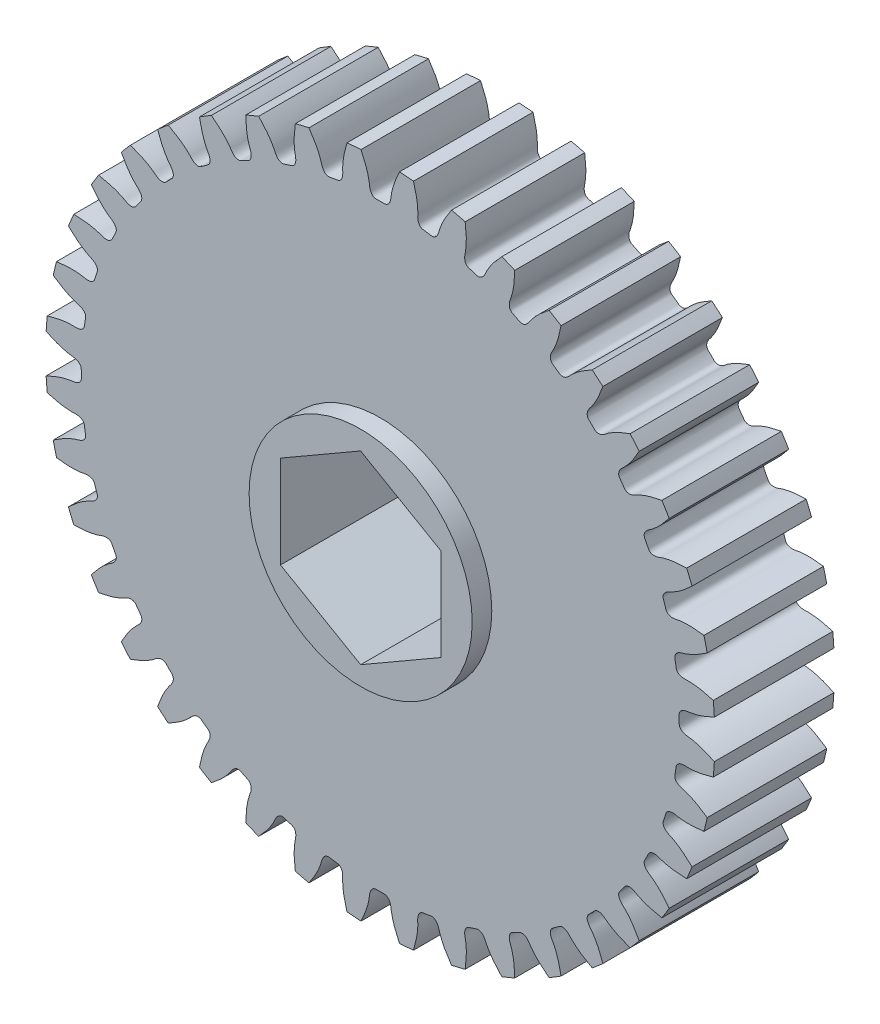
SolidWorks part; units mm, degrees
material "7075-T6 (SN)"
ref_plane "Front Plane" through (0, 0, 0) normal (0, 0, 1) x (1, 0, 0)
ref_plane "Top Plane" through (0, 0, 0) normal (0, 1, 0) x (1, 0, 0)
ref_plane "Right Plane" through (0, 0, 0) normal (1, 0, 0) x (0, 0, -1)
ref_plane "Plane1" through (0, 0, -4.7625) normal (0, 0, -1) x (-1, 0, 0)
sketch "Sketch1" plane through (0, 0, -4.7625) normal (0, 0, -1) x (-1, 0, 0)
  arc A0 (-25.7968, 6.7684) -> (-26.058, 5.6808) centre (0, 0) ccw
  arc A1 (-26.5381, 2.6496) -> (-26.6258, 1.5345) centre (0, 0) ccw
  arc A2 (-26.6258, -1.5345) -> (-26.5381, -2.6496) centre (0, 0) ccw
  arc A3 (-26.058, -5.6808) -> (-25.7968, -6.7684) centre (0, 0) ccw
  arc A4 (-24.8485, -9.6872) -> (-24.4204, -10.7206) centre (0, 0) ccw
  arc A5 (-23.0271, -13.4551) -> (-22.4427, -14.4088) centre (0, 0) ccw
  arc A6 (-20.6388, -16.8917) -> (-19.9124, -17.7422) centre (0, 0) ccw
  arc A7 (-17.7422, -19.9124) -> (-16.8917, -20.6388) centre (0, 0) ccw
  arc A8 (-14.4088, -22.4427) -> (-13.4551, -23.0271) centre (0, 0) ccw
  arc A9 (-10.7206, -24.4204) -> (-9.6872, -24.8485) centre (0, 0) ccw
  arc A10 (-6.7684, -25.7968) -> (-5.6808, -26.058) centre (0, 0) ccw
  arc A11 (-2.6496, -26.5381) -> (-1.5345, -26.6258) centre (0, 0) ccw
  arc A12 (1.5345, -26.6258) -> (2.6496, -26.5381) centre (0, 0) ccw
  arc A13 (5.6808, -26.058) -> (6.7684, -25.7968) centre (0, 0) ccw
  arc A14 (9.6872, -24.8485) -> (10.7206, -24.4204) centre (0, 0) ccw
  arc A15 (13.4551, -23.0271) -> (14.4088, -22.4427) centre (0, 0) ccw
  arc A16 (16.8917, -20.6388) -> (17.7422, -19.9124) centre (0, 0) ccw
  arc A17 (19.9124, -17.7422) -> (20.6388, -16.8917) centre (0, 0) ccw
  arc A18 (22.4427, -14.4088) -> (23.0271, -13.4551) centre (0, 0) ccw
  arc A19 (24.4204, -10.7206) -> (24.8485, -9.6872) centre (0, 0) ccw
  arc A20 (25.7968, -6.7684) -> (26.058, -5.6808) centre (0, 0) ccw
  arc A21 (26.5381, -2.6496) -> (26.6258, -1.5345) centre (0, 0) ccw
  arc A22 (26.6258, 1.5345) -> (26.5381, 2.6496) centre (0, 0) ccw
  arc A23 (26.058, 5.6808) -> (25.7968, 6.7684) centre (0, 0) ccw
  arc A24 (24.8485, 9.6872) -> (24.4204, 10.7206) centre (0, 0) ccw
  arc A25 (23.0271, 13.4551) -> (22.4427, 14.4088) centre (0, 0) ccw
  arc A26 (20.6388, 16.8917) -> (19.9124, 17.7422) centre (0, 0) ccw
  arc A27 (17.7422, 19.9124) -> (16.8917, 20.6388) centre (0, 0) ccw
  arc A28 (14.4088, 22.4427) -> (13.4551, 23.0271) centre (0, 0) ccw
  arc A29 (10.7206, 24.4204) -> (9.6872, 24.8485) centre (0, 0) ccw
  arc A30 (6.7684, 25.7968) -> (5.6808, 26.058) centre (0, 0) ccw
  arc A31 (2.6496, 26.5381) -> (1.5345, 26.6258) centre (0, 0) ccw
  arc A32 (-1.5345, 26.6258) -> (-2.6496, 26.5381) centre (0, 0) ccw
  arc A33 (-5.6808, 26.058) -> (-6.7684, 25.7968) centre (0, 0) ccw
  arc A34 (-9.6872, 24.8485) -> (-10.7206, 24.4204) centre (0, 0) ccw
  arc A35 (-13.4551, 23.0271) -> (-14.4088, 22.4427) centre (0, 0) ccw
  arc A36 (-16.8917, 20.6388) -> (-17.7422, 19.9124) centre (0, 0) ccw
  arc A37 (-19.9124, 17.7422) -> (-20.6388, 16.8917) centre (0, 0) ccw
  arc A38 (-22.4427, 14.4088) -> (-23.0271, 13.4551) centre (0, 0) ccw
  arc A39 (-24.4204, 10.7206) -> (-24.8485, 9.6872) centre (0, 0) ccw
  spline S0 degree 3 number of poles 87 (-25.7968, 6.7684) -> (-24.8485, 9.6872)
  spline S1 degree 3 number of poles 87 (-26.5381, 2.6496) -> (-26.058, 5.6808)
  spline S2 degree 3 number of poles 87 (-26.6258, -1.5345) -> (-26.6258, 1.5345)
  spline S3 degree 3 number of poles 87 (-26.058, -5.6808) -> (-26.5381, -2.6496)
  spline S4 degree 3 number of poles 87 (-24.8485, -9.6872) -> (-25.7968, -6.7684)
  spline S5 degree 3 number of poles 87 (-23.0271, -13.4551) -> (-24.4204, -10.7206)
  spline S6 degree 3 number of poles 87 (-20.6388, -16.8917) -> (-22.4427, -14.4088)
  spline S7 degree 3 number of poles 87 (-17.7422, -19.9124) -> (-19.9124, -17.7422)
  spline S8 degree 3 number of poles 87 (-14.4088, -22.4427) -> (-16.8917, -20.6388)
  spline S9 degree 3 number of poles 87 (-10.7206, -24.4204) -> (-13.4551, -23.0271)
  spline S10 degree 3 number of poles 87 (-6.7684, -25.7968) -> (-9.6872, -24.8485)
  spline S11 degree 3 number of poles 87 (-2.6496, -26.5381) -> (-5.6808, -26.058)
  spline S12 degree 3 number of poles 87 (1.5345, -26.6258) -> (-1.5345, -26.6258)
  spline S13 degree 3 number of poles 87 (5.6808, -26.058) -> (2.6496, -26.5381)
  spline S14 degree 3 number of poles 87 (9.6872, -24.8485) -> (6.7684, -25.7968)
  spline S15 degree 3 number of poles 87 (13.4551, -23.0271) -> (10.7206, -24.4204)
  spline S16 degree 3 number of poles 87 (16.8917, -20.6388) -> (14.4088, -22.4427)
  spline S17 degree 3 number of poles 87 (19.9124, -17.7422) -> (17.7422, -19.9124)
  spline S18 degree 3 number of poles 87 (22.4427, -14.4088) -> (20.6388, -16.8917)
  spline S19 degree 3 number of poles 87 (24.4204, -10.7206) -> (23.0271, -13.4551)
  spline S20 degree 3 number of poles 87 (25.7968, -6.7684) -> (24.8485, -9.6872)
  spline S21 degree 3 number of poles 87 (26.5381, -2.6496) -> (26.058, -5.6808)
  spline S22 degree 3 number of poles 87 (26.6258, 1.5345) -> (26.6258, -1.5345)
  spline S23 degree 3 number of poles 87 (26.058, 5.6808) -> (26.5381, 2.6496)
  spline S24 degree 3 number of poles 87 (24.8485, 9.6872) -> (25.7968, 6.7684)
  spline S25 degree 3 number of poles 87 (23.0271, 13.4551) -> (24.4204, 10.7206)
  spline S26 degree 3 number of poles 87 (20.6388, 16.8917) -> (22.4427, 14.4088)
  spline S27 degree 3 number of poles 87 (17.7422, 19.9124) -> (19.9124, 17.7422)
  spline S28 degree 3 number of poles 87 (14.4088, 22.4427) -> (16.8917, 20.6388)
  spline S29 degree 3 number of poles 87 (10.7206, 24.4204) -> (13.4551, 23.0271)
  spline S30 degree 3 number of poles 87 (6.7684, 25.7968) -> (9.6872, 24.8485)
  spline S31 degree 3 number of poles 87 (2.6496, 26.5381) -> (5.6808, 26.058)
  spline S32 degree 3 number of poles 87 (-1.5345, 26.6258) -> (1.5345, 26.6258)
  spline S33 degree 3 number of poles 87 (-5.6808, 26.058) -> (-2.6496, 26.5381)
  spline S34 degree 3 number of poles 87 (-9.6872, 24.8485) -> (-6.7684, 25.7968)
  spline S35 degree 3 number of poles 87 (-13.4551, 23.0271) -> (-10.7206, 24.4204)
  spline S36 degree 3 number of poles 87 (-16.8917, 20.6388) -> (-14.4088, 22.4427)
  spline S37 degree 3 number of poles 87 (-19.9124, 17.7422) -> (-17.7422, 19.9124)
  spline S38 degree 3 number of poles 87 (-22.4427, 14.4088) -> (-20.6388, 16.8917)
  spline S39 degree 3 number of poles 87 (-24.4204, 10.7206) -> (-23.0271, 13.4551)
extrude "Boss-Extrude1" add sketch "Sketch1" against normal blind 9.525
sketch "Sketch2" plane through (0, 0, -4.7625) normal (0, 0, -1) x (-1, 0, 0)
  circle A0 centre (0, 0) radius 8.89
extrude "Boss-Extrude2" add sketch "Sketch2" along normal blind 1.5621
sketch "Sketch3" plane through (0, 0, 4.7625) normal (0, 0, 1) x (1, 0, 0)
  circle A0 centre (0, 0) radius 8.89
extrude "Boss-Extrude3" add sketch "Sketch3" along normal blind 1.5621
sketch "Sketch4" plane through (0, 0, 6.3246) normal (0, 0, 1) x (1, 0, 0)
  line L0 (6.3881, -3.6882) -> (6.3881, 3.6882)
  line L1 (6.3881, 3.6882) -> (0, 7.3763)
  line L2 (0, 7.3763) -> (-6.3881, 3.6882)
  line L3 (-6.3881, 3.6882) -> (-6.3881, -3.6882)
  line L4 (-6.3881, -3.6882) -> (0, -7.3763)
  line L5 (0, -7.3763) -> (6.3881, -3.6882)
extrude "Cut-Extrude1" cut sketch "Sketch4" against normal through all
